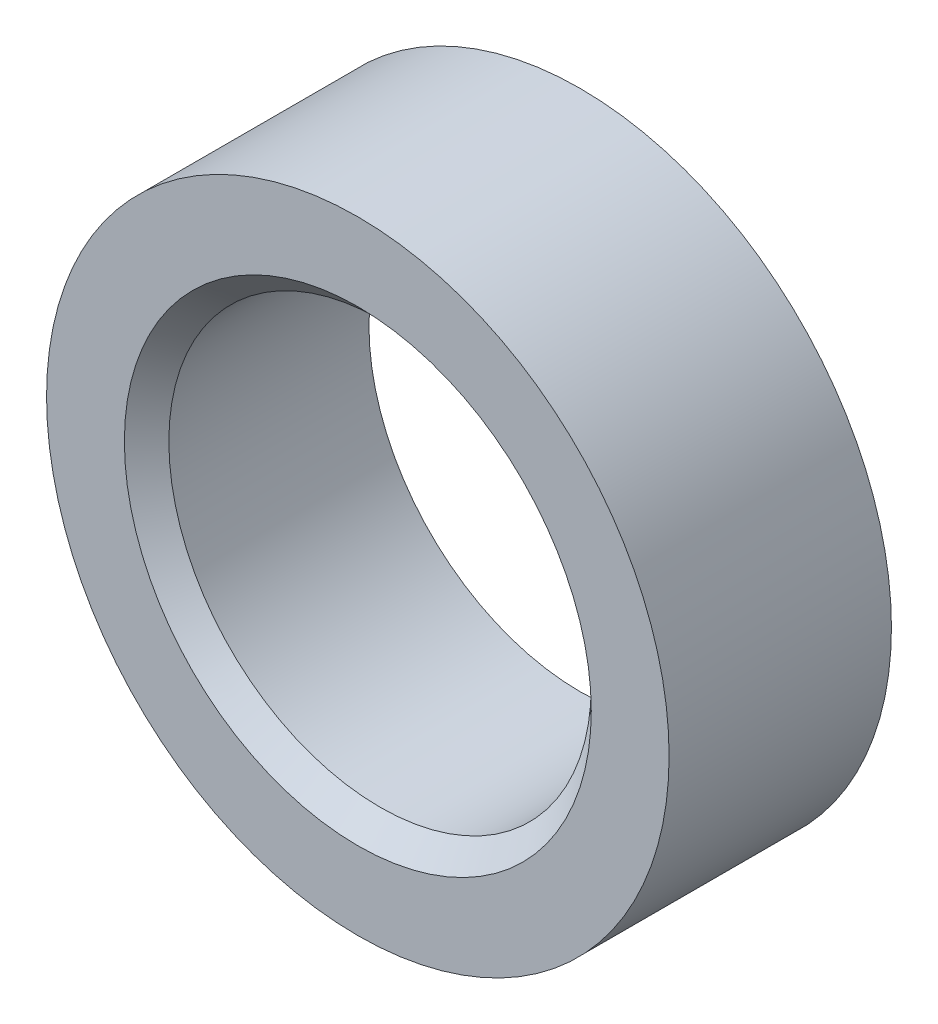
SolidWorks part; units mm, degrees
ref_plane "Front Plane" through (0, 0, 0) normal (0, 0, 1) x (1, 0, 0)
ref_plane "Top Plane" through (0, 0, 0) normal (0, 1, 0) x (1, 0, 0)
ref_plane "Right Plane" through (0, 0, 0) normal (1, 0, 0) x (0, 0, -1)
sketch "Sketch1" plane through (0, 0, 0) normal (0, 0, 1) x (1, 0, 0)
  circle A0 centre (0, 0) radius 9.5
  circle A1 centre (0, 0) radius 14
  dimension "D1" = 19
  dimension "D2" = 28
extrude "Boss-Extrude1" add sketch "Sketch1" along normal blind 10
chamfer "Chamfer1" distance 1 angle 45 1 edges at (9.5, 0, 10)
